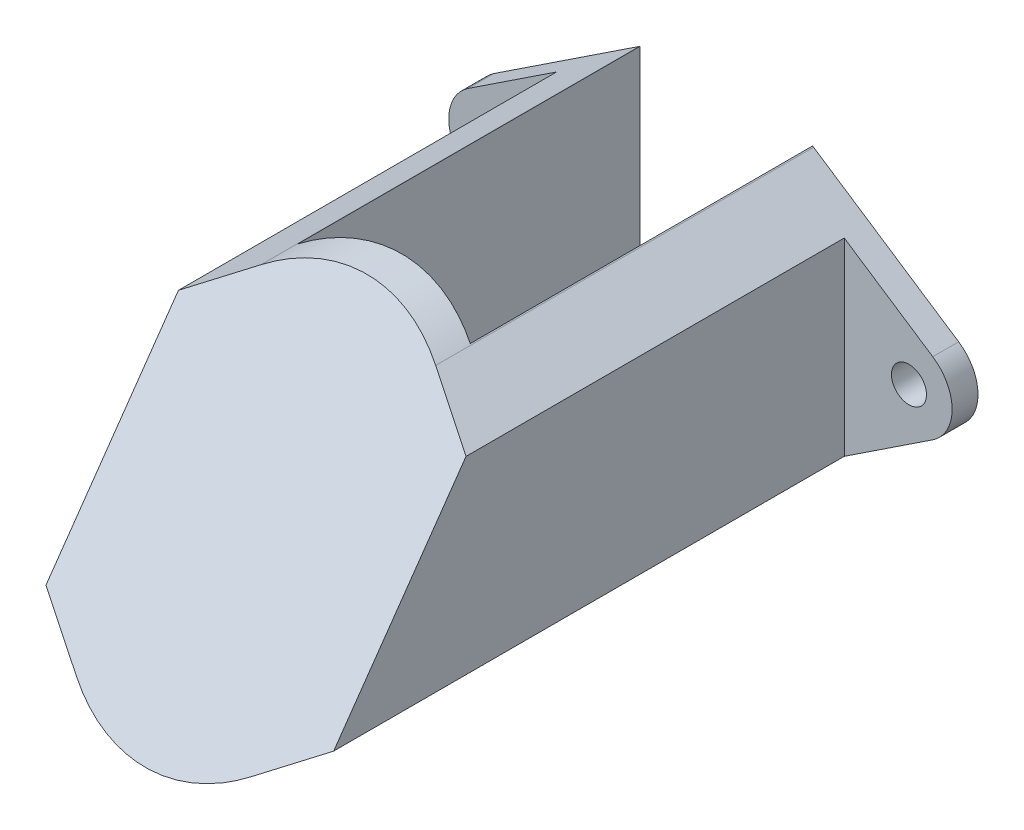
SolidWorks part; units mm, degrees
ref_plane "Front Plane" through (0, 0, 0) normal (0, 0, 1) x (1, 0, 0)
ref_plane "Top Plane" through (0, 0, 0) normal (0, 1, 0) x (1, 0, 0)
ref_plane "Right Plane" through (0, 0, 0) normal (1, 0, 0) x (0, 0, -1)
sketch "Sketch1" plane through (0, 0, 0) normal (0, 0, 1) x (1, 0, 0)
  line L0 (-14.5, 0) -> (14.5, 0) construction
  line L1 (-16.1552, 2.5021) -> (-6.069, 9.1743)
  line L2 (6.069, 9.1743) -> (16.1552, 2.5021)
  line L5 (16.1552, -2.5021) -> (6.069, -9.1743)
  line L6 (-6.069, -9.1743) -> (-16.1552, -2.5021)
  arc A0 (-6.069, -9.1743) -> (6.069, -9.1743) centre (0, 0) ccw
  arc A1 (16.1552, -2.5021) -> (16.1552, 2.5021) centre (14.5, 0) ccw
  arc A2 (-16.1552, 2.5021) -> (-16.1552, -2.5021) centre (-14.5, 0) ccw
  arc A3 (6.069, 9.1743) -> (-6.069, 9.1743) centre (0, 0) ccw
  dimension "D1" = 6
  dimension "D2" = 22
  dimension "D3" = 29
extrude "Boss-Extrude1" add sketch "Sketch1" along normal blind 45
sketch "Sketch3" plane through (0, 0, 0) normal (1, 0, 0) x (0, 0, -1)
  line L0 (-25, 11) -> (-40.4046, -11)
  line L1 (0, 11) -> (-45, 11) construction
  line L2 (-45, -11) -> (0, -11) construction
  line L3 (-40.4046, -11) -> (0, -11)
  line L4 (0, -11) -> (0, 11)
  line L5 (0, 11) -> (-25, 11)
  dimension "D1" = 35
  dimension "D2" = 25
extrude "Cut-Extrude1" cut sketch "Sketch3" against normal through all both and the other way through all flip side to cut
sketch "Sketch5" plane through (0, 0, 0) normal (0, 0, -1) x (-1, 0, 0)
  line L1 (-10, -12.207) -> (10, -12.207)
  line L2 (-10, -12.207) -> (-10, 12.207)
  line L3 (-10, 12.207) -> (10, 12.207)
  line L4 (10, -12.207) -> (10, 12.207)
  line L5 (-10, -12.207) -> (10, 12.207) construction
  line L6 (-10, 12.207) -> (10, -12.207) construction
  point P0 (0, 0)
  dimension "D1" = 20
extrude "Cut-Extrude2" cut sketch "Sketch5" against normal through all from offset 1.8 flip side to cut offset against normal yes
hole_wizard "#2 Clearance Hole1" positions "Sketch6" profile "Sketch7" hole size "#2" standard "ANSI Inch" end condition through all
sketch "Sketch6" plane through (0, 0, 1.8) normal (0, 0, 1) x (1, 0, 0)
  arc A0 (16.1552, -2.5021) -> (16.1552, 2.5021) centre (14.5, 0) ccw construction
  arc A1 (-16.1552, 2.5021) -> (-16.1552, -2.5021) centre (-14.5, 0) ccw construction
  point P0 (14.5, 0)
  point P2 (-14.5, 0)
sketch "Sketch7" plane through (14.5, 0, 1.8) normal (1, 0, 0) x (0, -1, 0)
  line L0 (0, 0) -> (0, 1.8)
  line L1 (0, 1.8) -> (1.2192, 1.8)
  line L2 (1.2192, 1.8) -> (1.2192, 0)
  line L5 (1.2192, 0) -> (0, 0)
  line L11 (0, -6.35) -> (0, 107.95) construction
  dimension "Thru Hole Dia." = 2.4384
  dimension "Thru Hole Depth" = 1.8
sketch "Sketch8" plane through (0, 15.365, 21.9436) normal (0, 0.5736, 0.8192) x (1, 0, 0)
  line L0 (-10, -10.7321) -> (-10, -26.7824) construction
  line L1 (6, 32.1858) -> (-6, 32.1858)
  line L2 (6, 32.1858) -> (6, -32.1858)
  line L3 (6, -32.1858) -> (-6, -32.1858)
  line L4 (-6, 32.1858) -> (-6, -32.1858)
  line L5 (6, 32.1858) -> (-6, -32.1858) construction
  line L6 (6, -32.1858) -> (-6, 32.1858) construction
  ellipse E0 centre (0, -18.7573) end of major axis (0, -32.1858) minor radius 11 (-6.069, -29.957) -> (6.069, -29.957) ccw construction
  point P0 (0, 0)
  dimension "D1" = 4
extrude "Cut-Extrude3" cut sketch "Sketch8" against normal through all from offset 2
